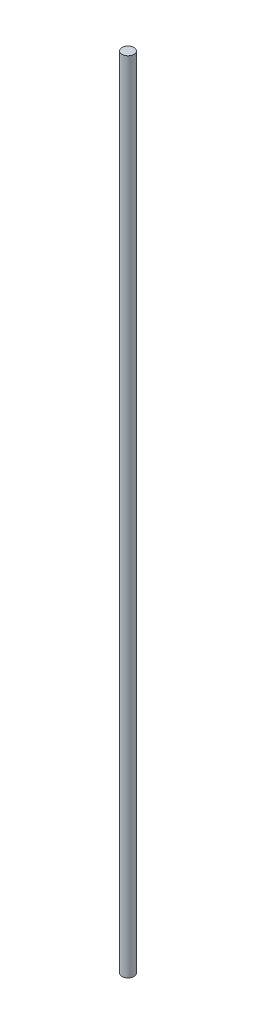
SolidWorks part; units mm, degrees
ref_plane "Front Plane" through (0, 0, 0) normal (0, 0, 1) x (1, 0, 0)
ref_plane "Top Plane" through (0, 0, 0) normal (0, 1, 0) x (1, 0, 0)
ref_plane "Right Plane" through (0, 0, 0) normal (1, 0, 0) x (0, 0, -1)
sketch "Sketch1" plane through (0, 0, 0) normal (0, 1, 0) x (1, 0, 0)
  circle A0 centre (0, 0) radius 0.75
  dimension "D1" = 1.5
extrude "Boss-Extrude1" add sketch "Sketch1" along normal blind 100
